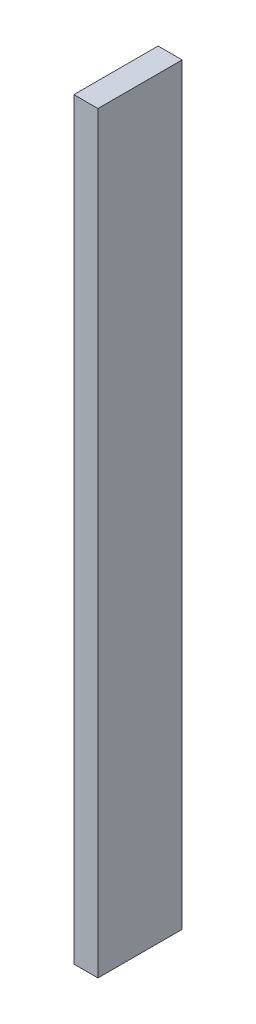
SolidWorks part; units mm, degrees
material "Chêne"
ref_plane "Plan de face" through (0, 0, 0) normal (0, 0, 1) x (1, 0, 0)
ref_plane "Plan de dessus" through (0, 0, 0) normal (0, 1, 0) x (1, 0, 0)
ref_plane "Plan de droite" through (0, 0, 0) normal (1, 0, 0) x (0, 0, -1)
sketch "Esquisse1" plane through (0, 0, 0) normal (0, 0, 1) x (1, 0, 0)
  line L1 (52.65, 157) -> (62.65, 157)
  line L2 (52.65, 157) -> (52.65, -156)
  line L3 (52.65, -156) -> (62.65, -156)
  line L4 (62.65, 157) -> (62.65, -156)
  line L6 (52.15, 156.3) -> (52.15, -126.7) construction
  line L7 (118, -161) -> (-900, -161) construction
  line L8 (-900, 162) -> (68, 162) construction
  point P7 (57.65, -156)
  dimension "D1" = 10
  dimension "D2" = 0.5
  dimension "D3" = 5
  dimension "D4" = 5
extrude "Boss.-Extru.1" add sketch "Esquisse1" along normal blind 35 contours L4 L3 L2 L1
